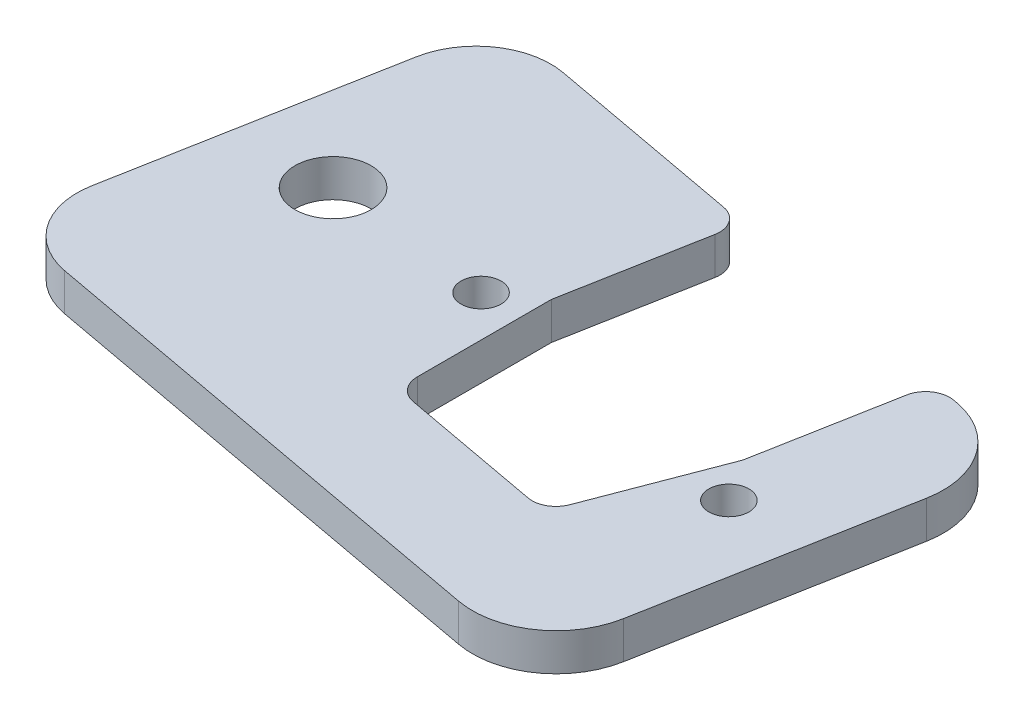
SolidWorks part; units mm, degrees
ref_plane "Front Plane" through (0, 0, 0) normal (0, 0, 1) x (1, 0, 0)
ref_plane "Top Plane" through (0, 0, 0) normal (0, 1, 0) x (1, 0, 0)
ref_plane "Right Plane" through (0, 0, 0) normal (1, 0, 0) x (0, 0, -1)
sketch "Sketch1" plane through (0, 0, 0) normal (0, 1, 0) x (1, 0, 0)
  line L0 (-26.3858, 2.6924) -> (-9.6505, -0.397)
  line L1 (-8.5253, -27.8933) -> (3.4348, -30.1012)
  line L2 (5.7017, -28.8285) -> (9.7689, -18.1881)
  line L3 (14.3033, -4.8191) -> (14.678, -4.8883)
  line L4 (20.3807, -13.1732) -> (16.3621, -34.9415)
  line L5 (8.0771, -40.6442) -> (-32.9866, -33.0635)
  line L6 (-38.0783, -25.6662) -> (-33.783, -2.3993)
  line L7 (-8.0212, -2.7641) -> (-10.1884, -14.5038)
  line L8 (14.4591, -30.4187) -> (17.2319, -15.399) construction
  line L9 (11.92, -6.5359) -> (9.7689, -18.1881) construction
  line L10 (-10.1884, -14.5038) -> (-10.1884, -25.8951)
  line L11 (9.7689, -18.1881) -> (11.9362, -6.4484)
  line L12 (9.7689, -18.1881) -> (5.7281, -28.7594) construction
  line L13 (-10.1884, -25.8211) -> (-10.1884, -14.5038) construction
  line L14 (12.1459, -21.7522) -> (-13.6813, -16.9843) construction
  line L15 (-35.9307, -14.0327) -> (-27.6879, -15.5544) construction
  line L18 (-10.1884, -14.5038) -> (-8.0373, -2.8516) construction
  line L19 (-11.8691, -34.5211) -> (4.1917, -37.486) construction
  arc A0 (1.6614, -27.6171) -> (5.7281, -28.7594) centre (3.747, -28.0021) ccw construction
  arc A1 (-9.6505, -0.397) -> (-8.0212, -2.7641) centre (-10.0194, -2.3953) cw
  arc A2 (11.9362, -6.4484) -> (14.3033, -4.8191) centre (13.9344, -6.8173) cw
  arc A3 (-8.5253, -27.8933) -> (-10.1884, -25.8951) centre (-8.1564, -25.8951) cw
  arc A4 (3.4348, -30.1012) -> (5.7017, -28.8285) centre (3.8037, -28.103) ccw
  arc A5 (14.678, -4.8883) -> (20.3807, -13.1732) centre (13.3869, -11.8821) cw
  arc A6 (16.3621, -34.9415) -> (8.0771, -40.6442) centre (9.3683, -33.6504) cw
  circle A7 centre (12.1459, -21.7522) radius 1.7018
  circle A8 centre (-13.6813, -16.9843) radius 1.7018
  arc A9 (14.3907, -4.8352) -> (11.92, -6.5359) centre (14.0057, -6.9209) ccw construction
  circle A10 centre (-13.6813, -16.9843) radius 1.7018 construction
  arc A11 (-32.9866, -33.0635) -> (-38.0783, -25.6662) centre (-31.8338, -26.819) cw
  arc A12 (-26.3858, 2.6924) -> (-33.783, -2.3993) centre (-27.5385, -3.5521) ccw
  circle A13 centre (12.1459, -21.7522) radius 1.7018 construction
  circle A14 centre (-27.6879, -15.5544) radius 3.2385
  spline S0 degree 3 poles (-9.738, -0.3809) (-13.0249, 0.2259) (-15.7225, -6.8445) (-16.1636, -9.2339) knots 0 0 0 0 1 1 1 1 construction
  dimension "D2" = 2.032
  dimension "D1" = 2.032
  dimension "D4" = 7.112
  dimension "D5" = 7.112
  dimension "D6" = 9.525
  dimension "D7" = 6.35
  dimension "D9" = 6.477
  dimension "D3" = 9.525
  dimension "D8" = 25.4
  dimension "D10" = 8.382
extrude "Boss-Extrude1" add sketch "Sketch1" along normal blind 3.175
